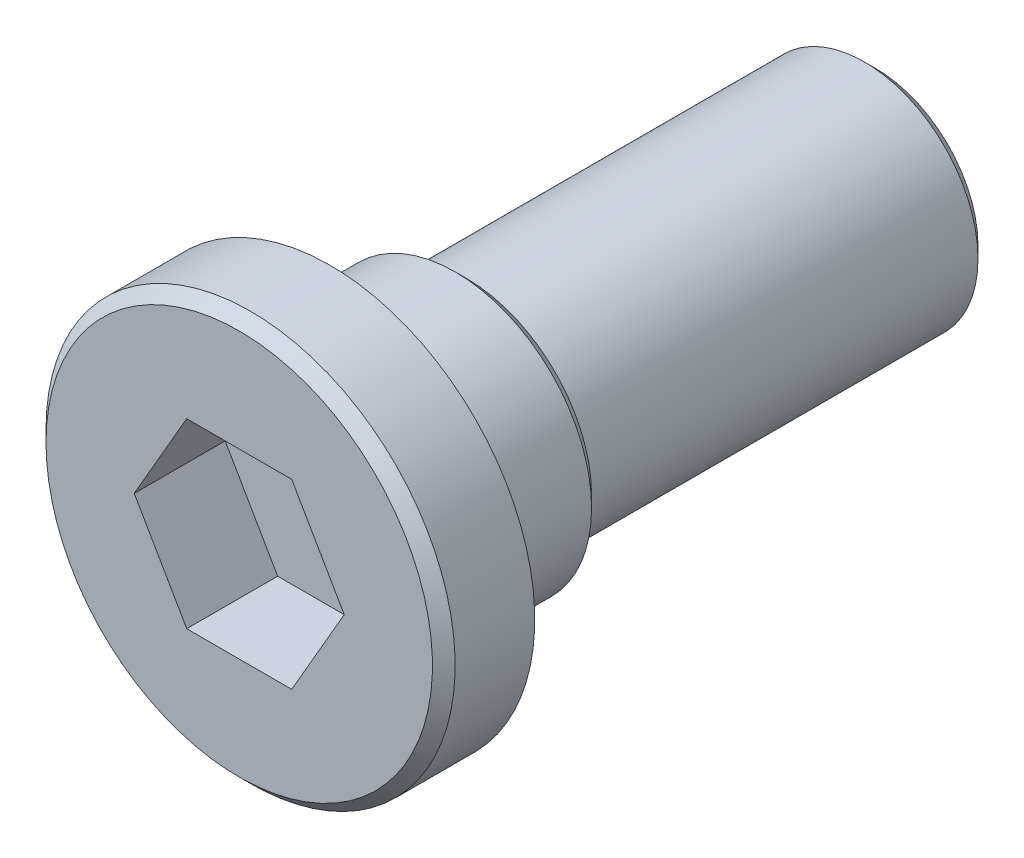
SolidWorks part; units mm, degrees
material "Plain Carbon Steel"
ref_plane "Front" through (0, 0, 0) normal (0, 0, 1) x (1, 0, 0)
ref_plane "Top" through (0, 0, 0) normal (0, 1, 0) x (1, 0, 0)
ref_plane "Right" through (0, 0, 0) normal (1, 0, 0) x (0, 0, -1)
sketch "Sketch1" plane through (0, 0, 0) normal (0, 1, 0) x (1, 0, 0)
  line L0 (0, 0) -> (0, 7)
  line L1 (0, 7) -> (1.25, 7)
  line L2 (1.25, 7) -> (1.25, 2.5)
  line L3 (1.25, 2.5) -> (1.5, 2.5)
  line L4 (1.5, 2.5) -> (1.5, 1)
  line L5 (1.5, 1) -> (2.25, 1)
  line L6 (2.25, 1) -> (2.25, 0)
  line L7 (2.25, 0) -> (0, 0)
  line L8 (0, 0) -> (0, -13.5621) construction
  dimension "D1" = 2.5
  dimension "D2" = 3
  dimension "D3" = 4.5
  dimension "D4" = 1
  dimension "D5" = 1.5
  dimension "D6" = 7
revolve "Revolve1" add sketch "Sketch1" angle 360 about L8
sketch "Sketch2" plane through (0, 0, 0) normal (0, 0, 1) x (1, 0, 0)
  line L1 (1.1547, 0) -> (0.5774, 1)
  line L2 (0.5774, 1) -> (-0.5774, 1)
  line L3 (-0.5774, 1) -> (-1.1547, 0)
  line L4 (-1.1547, 0) -> (-0.5774, -1)
  line L5 (-0.5774, -1) -> (0.5774, -1)
  line L6 (0.5774, -1) -> (1.1547, 0)
  circle A0 centre (0, 0) radius 1 construction
  dimension "D1" = 2
extrude "Cut-Extrude1" cut sketch "Sketch2" against normal blind 1
chamfer "Chamfer1" distance 0.125 3 edges at (-1.5, 0, -2.5) (-1.25, 0, -7) (-2.25, 0, 0)
